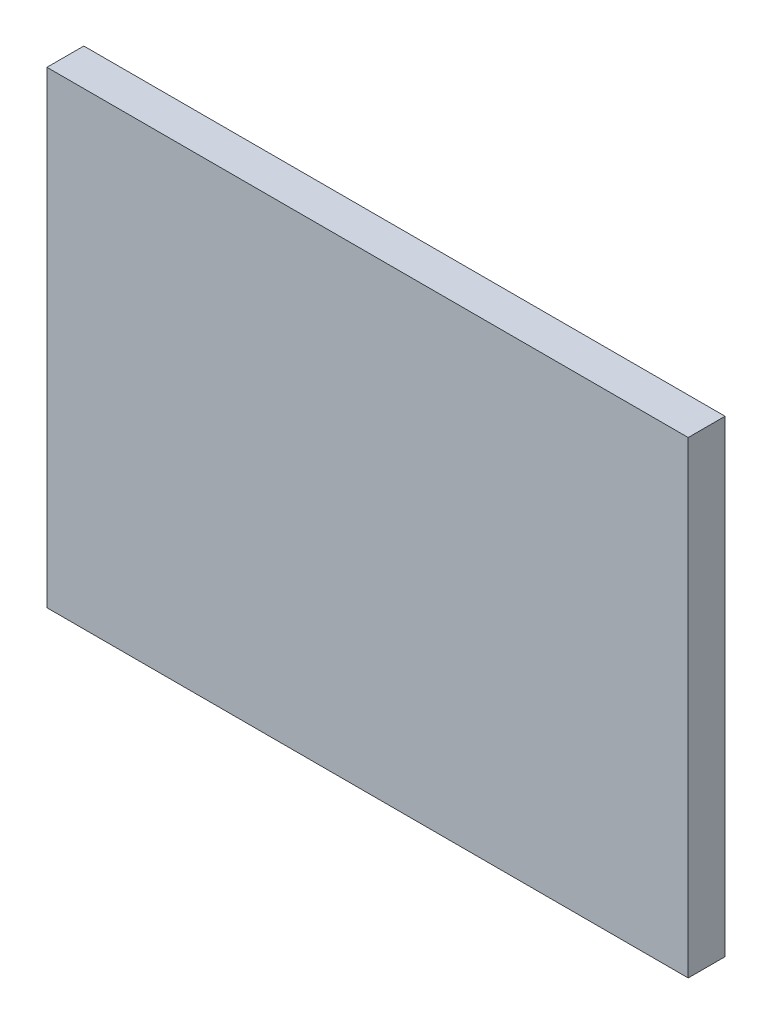
SolidWorks part; units mm, degrees
ref_plane "Front Plane" through (0, 0, 0) normal (0, 0, 1) x (1, 0, 0)
ref_plane "Top Plane" through (0, 0, 0) normal (0, 1, 0) x (1, 0, 0)
ref_plane "Right Plane" through (0, 0, 0) normal (1, 0, 0) x (0, 0, -1)
sketch "Sketch1" plane through (0, 0, 0) normal (0, 0, 1) x (1, 0, 0)
  line L0 (0, 40.7768) -> (0, -37.1492) construction
  line L1 (-44.6059, 0) -> (52.8016, 0) construction
  line L2 (-34.798, -25.4) -> (-34.798, 25.4)
  line L3 (-34.798, 25.4) -> (34.798, 25.4)
  line L4 (34.798, -25.4) -> (34.798, 25.4)
  line L5 (-34.798, -25.4) -> (34.798, -25.4)
  point P5 (0, -25.4)
  point P9 (0, 25.4)
  point P11 (34.798, 0)
  point P12 (-34.798, 0)
  dimension "D1" = 69.596
  dimension "D2" = 50.8
extrude "Boss-Extrude1" add sketch "Sketch1" along normal blind 4
